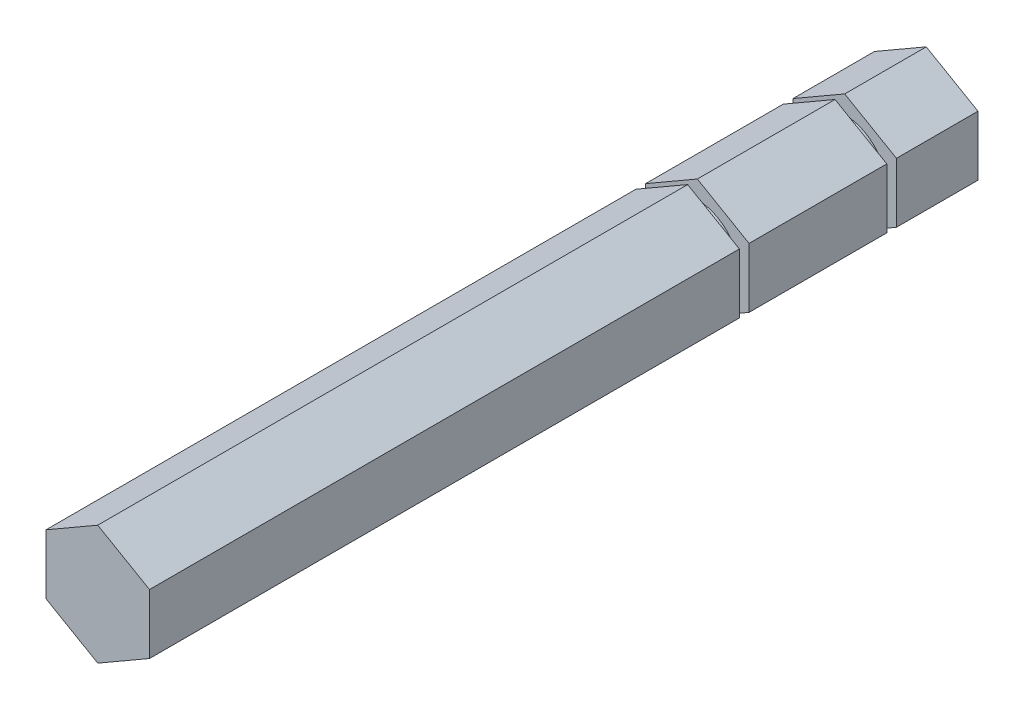
SolidWorks part; units mm, degrees
ref_plane "Front Plane" through (0, 0, 0) normal (0, 0, 1) x (1, 0, 0)
ref_plane "Top Plane" through (0, 0, 0) normal (0, 1, 0) x (1, 0, 0)
ref_plane "Right Plane" through (0, 0, 0) normal (1, 0, 0) x (0, 0, -1)
sketch "Sketch1" plane through (0, 0, 0) normal (0, 0, 1) x (1, 0, 0)
  line L1 (0, 5.4993) -> (-4.7625, 2.7496)
  line L2 (-4.7625, 2.7496) -> (-4.7625, -2.7496)
  line L3 (-4.7625, -2.7496) -> (0, -5.4993)
  line L4 (0, -5.4993) -> (4.7625, -2.7496)
  line L5 (4.7625, -2.7496) -> (4.7625, 2.7496)
  line L6 (4.7625, 2.7496) -> (0, 5.4993)
  circle A0 centre (0, 0) radius 4.7625 construction
  dimension "D1" = 9.525
extrude "Boss-Extrude1" add sketch "Sketch1" along normal blind 76.2508
ref_plane "Plane1" through (0, 0, 21.5138) normal (0, 0, -1) x (-1, 0, 0)
sketch "Sketch5" plane through (0, 0, 21.5138) normal (0, 0, -1) x (-1, 0, 0)
  line L1 (-5.93, -6.1669) -> (5.1735, -6.1669)
  line L2 (-5.93, -6.1669) -> (-5.93, 5.9781)
  line L3 (-5.93, 5.9781) -> (5.1735, 5.9781)
  line L4 (5.1735, -6.1669) -> (5.1735, 5.9781)
  circle A0 centre (0, 0) radius 3.8481
  dimension "D1" = 7.6962
extrude "Cut-Extrude2" cut sketch "Sketch5" against normal mid plane 0.889
ref_plane "Plane2" through (0, 0, 7.9502) normal (0, 0, -1) x (-1, 0, 0)
sketch "Sketch6" plane through (0, 0, 7.9502) normal (0, 0, -1) x (-1, 0, 0)
  line L1 (-5.642, -5.9402) -> (5.1101, -5.9402)
  line L2 (-5.642, -5.9402) -> (-5.642, 5.5695)
  line L3 (-5.642, 5.5695) -> (5.1101, 5.5695)
  line L4 (5.1101, -5.9402) -> (5.1101, 5.5695)
  circle A0 centre (0, 0) radius 3.8481
  dimension "D1" = 7.6962
extrude "Cut-Extrude3" cut sketch "Sketch6" against normal mid plane 0.889
